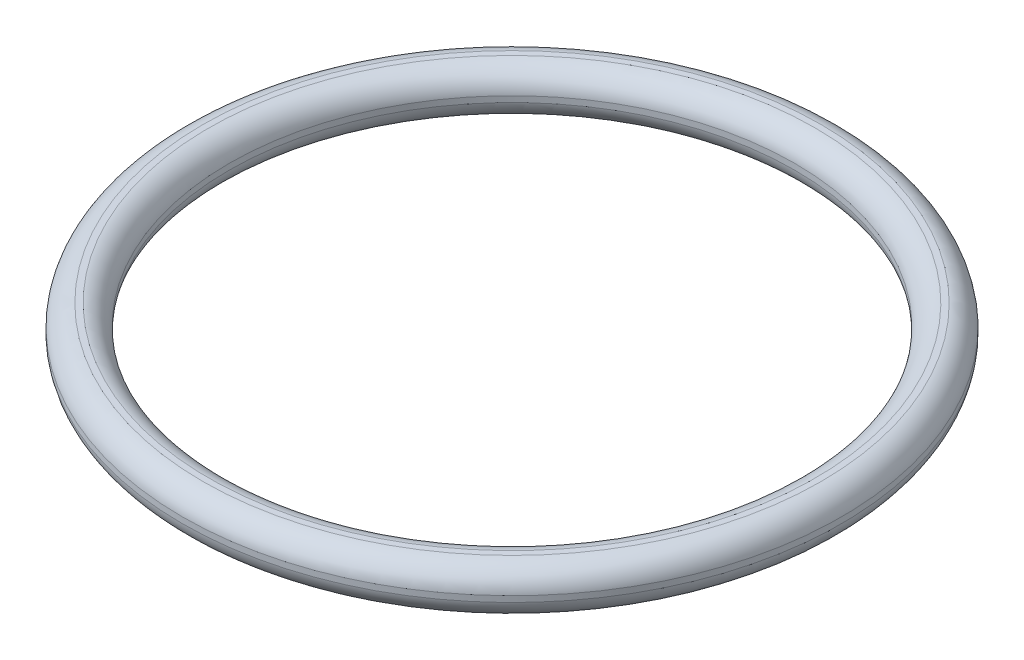
SolidWorks part; units mm, degrees
ref_plane "Front Plane" through (0, 0, 0) normal (0, 0, 1) x (1, 0, 0)
ref_plane "Top Plane" through (0, 0, 0) normal (0, 1, 0) x (1, 0, 0)
ref_plane "Right Plane" through (0, 0, 0) normal (1, 0, 0) x (0, 0, -1)
sketch "Sketch3" plane through (0, 0, 0) normal (0, 0, 1) x (1, 0, 0)
  line L0 (0, 0) -> (-41.275, 0)
  circle A0 centre (-41.275, 0) radius 3.175
  dimension "D2" = 6.35
  dimension "D1" = 41.275
ref_axis "Axis1" through (0, -2.75, 0) along (0, 1, 0)
revolve "Revolve1" add sketch "Sketch3" angle 360 about axis through (0, -2.75, 0) along (0, 1, 0)
sketch "Sketch6" plane through (0, 0, 0) normal (0, 0, 1) x (1, 0, 0)
  line L0 (0, -2.75) -> (0, 2.75) construction
  line L1 (0, 3.15) -> (-38.125, 3.15)
  line L2 (0, 3.15) -> (0, -3.15)
  line L3 (0, -3.15) -> (-38.125, -3.15)
  line L4 (-38.125, 3.15) -> (-38.125, -3.15)
  line L6 (-49.425, 3.15) -> (-44.425, 3.15)
  line L7 (-49.425, 3.15) -> (-49.425, -3.15)
  line L8 (-49.425, -3.15) -> (-44.425, -3.15)
  line L9 (-44.425, 3.15) -> (-44.425, -3.15)
  line L10 (-38.125, -8.15) -> (-44.425, -8.15)
  line L11 (-38.125, -8.15) -> (-38.125, -3.15)
  line L12 (-38.125, -3.15) -> (-44.425, -3.15)
  line L13 (-44.425, -8.15) -> (-44.425, -3.15)
  line L14 (-44.425, 8.15) -> (-38.125, 8.15)
  line L15 (-44.425, 8.15) -> (-44.425, 3.15)
  line L16 (-44.425, 3.15) -> (-38.125, 3.15)
  line L17 (-38.125, 8.15) -> (-38.125, 3.15)
  dimension "D1" = 38.125
  dimension "D2" = 6.3
  dimension "D3" = 6.3
  dimension "D4" = 3.15
  dimension "D5" = 5
  dimension "D6" = 5
  dimension "D7" = 5
revolve "Cut-Revolve1" cut sketch "Sketch6" angle 360 about axis through (0, -2.75, 0) along (0, 1, 0)
